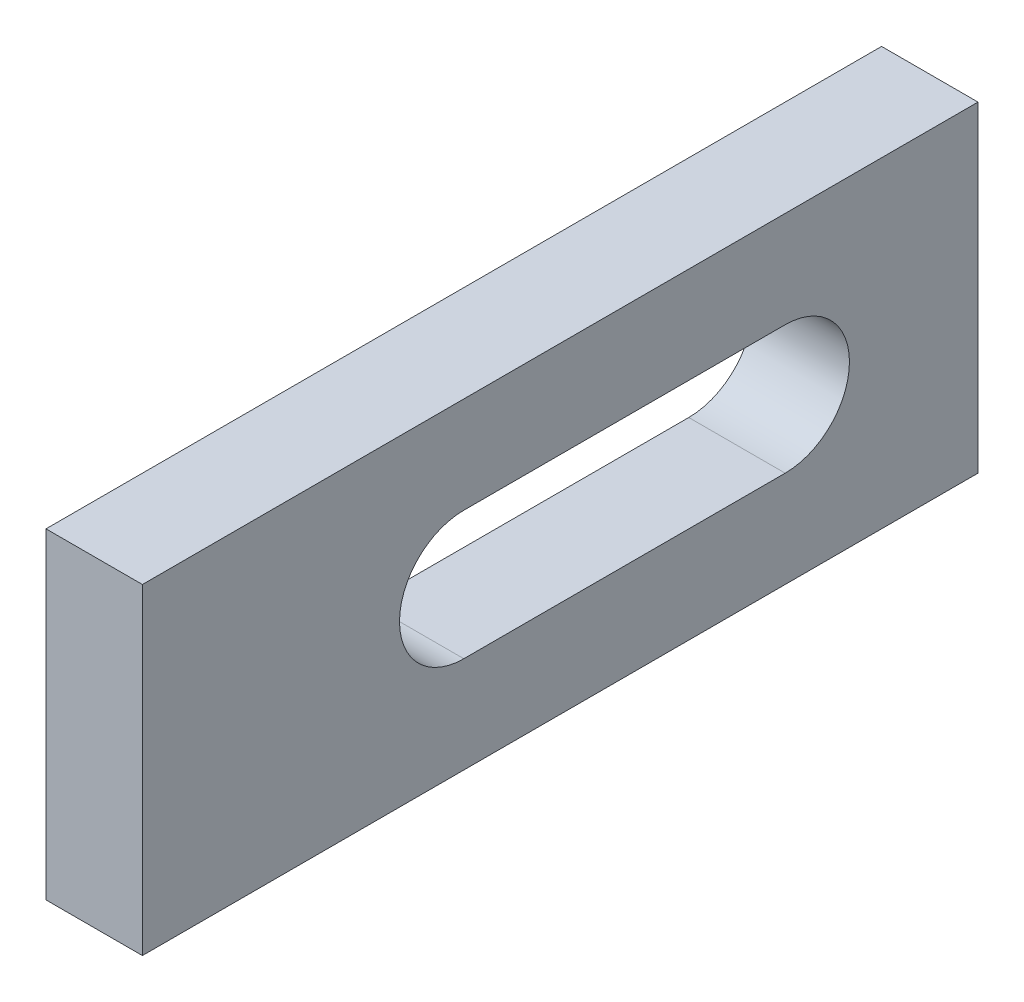
SolidWorks part; units mm, degrees
material "1.0038 (S235JRG2)"
ref_plane "Plan de face" through (0, 0, 0) normal (0, 0, 1) x (1, 0, 0)
ref_plane "Plan de dessus" through (0, 0, 0) normal (0, 1, 0) x (1, 0, 0)
ref_plane "Plan de droite" through (0, 0, 0) normal (1, 0, 0) x (0, 0, -1)
sketch "Esquisse1" plane through (0, 0, 0) normal (0, 0, 1) x (1, 0, 0)
  line L1 (-7.5, -25) -> (7.5, -25)
  line L2 (-7.5, -25) -> (-7.5, 25)
  line L3 (-7.5, 25) -> (7.5, 25)
  line L4 (7.5, -25) -> (7.5, 25)
  point P4 (0, -25)
  point P5 (-7.5, 0)
  dimension "D1" = 50
  dimension "D2" = 15
extrude "Boss.-Extru.1" add sketch "Esquisse1" along normal mid plane 130
sketch "Esquisse2" plane through (7.5, 0, 0) normal (1, 0, 0) x (0, 0, -1)
  line L2 (-15, 10) -> (35, 10)
  line L3 (65, -25) -> (65, 25) construction
  line L4 (35, -10) -> (-15, -10)
  line L6 (-65, 25) -> (65, 25) construction
  arc A0 (-15, 10) -> (-15, -10) centre (-15, 0) ccw
  arc A1 (35, -10) -> (35, 10) centre (35, 0) ccw
  dimension "D1" = 30
  dimension "D2" = 50
  dimension "D3" = 20
  dimension "D4" = 20
  dimension "D5" = 25
extrude "Enlèv. mat.-Extru.1" cut sketch "Esquisse2" against normal blind 110
